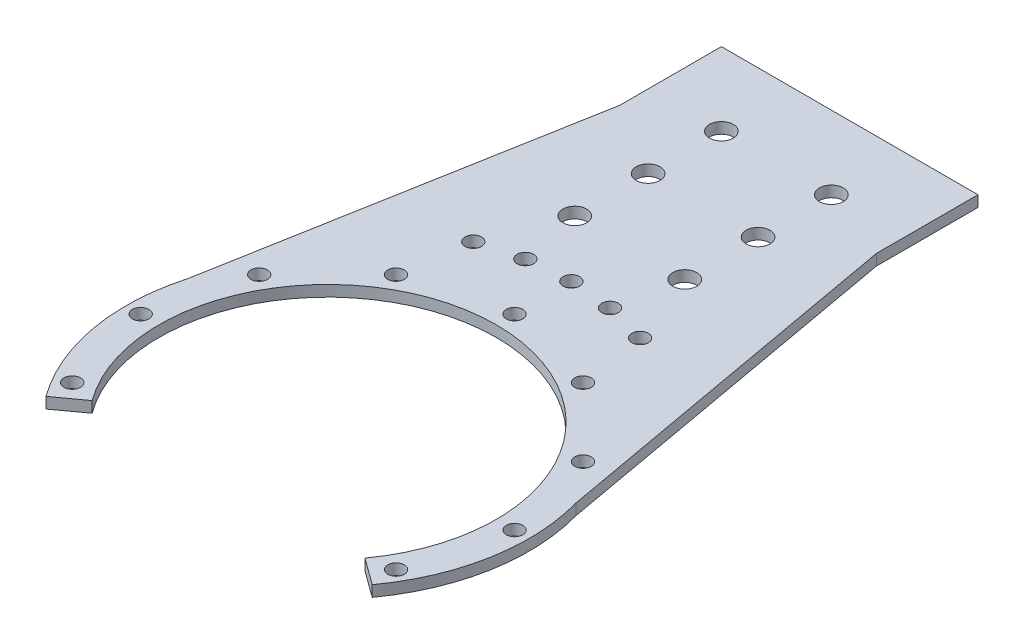
SolidWorks part; units mm, degrees
ref_plane "Front Plane" through (0, 0, 0) normal (0, 0, 1) x (1, 0, 0)
ref_plane "Top Plane" through (0, 0, 0) normal (0, 1, 0) x (1, 0, 0)
ref_plane "Right Plane" through (0, 0, 0) normal (1, 0, 0) x (0, 0, -1)
sketch "Sketch1" plane through (0, 0, 0) normal (0, 1, 0) x (1, 0, 0)
  circle A0 centre (0, 0) radius 55
  dimension "D1" = 110
extrude "Boss-Extrude1" add sketch "Sketch1" along normal blind 3
sketch "Sketch2" plane through (0, 0, 0) normal (0, 1, 0) x (1, 0, 0)
  line L0 (0, 0) -> (0, 92.4264) construction
  line L1 (-35, 142.4264) -> (-35, 42.4264)
  line L2 (-35, 142.4264) -> (35, 142.4264)
  line L3 (-35, 42.4264) -> (35, 42.4264)
  line L4 (35, 142.4264) -> (35, 42.4264)
  line L5 (0, 42.4264) -> (0, 142.4264) construction
  line L6 (-35, 92.4264) -> (35, 92.4264) construction
  circle A0 centre (0, 0) radius 55 construction
  dimension "D1" = 100
  dimension "D2" = 70
extrude "Boss-Extrude2" add sketch "Sketch2" along normal blind 3
sketch "Sketch9" plane through (0, 0, 0) normal (0, 1, 0) x (1, 0, 0)
  line L0 (-35, 114.7213) -> (-52.9849, 14.7514)
  line L1 (-35, 142.4264) -> (-35, 42.4264) construction
  line L2 (-52.9849, 14.7514) -> (-17.8715, 14.7514)
  line L3 (-17.8715, 14.7514) -> (-35, 114.7213)
  arc A0 (-35, 42.4264) -> (35, 42.4264) centre (0, 0) ccw construction
extrude "Boss-Extrude3" add sketch "Sketch9" along normal blind 3 contours L3 L0 L2
mirror "Mirror2" about plane through (0, 0, 0) normal (1, 0, 0) of "Boss-Extrude3"
sketch "Sketch4" plane through (0, 3, 0) normal (0, 1, 0) x (1, 0, 0)
  circle A0 centre (0, 0) radius 51 construction
  circle A1 centre (0, 0) radius 46
  dimension "D1" = 102
  dimension "D2" = 92
extrude "Cut-Extrude2" cut sketch "Sketch4" against normal through all both and the other way through all
sketch "Sketch7" plane through (0, 3, 0) normal (0, 1, 0) x (1, 0, 0)
  line L0 (0, 0) -> (0, -55)
  line L1 (0, 0) -> (-44.4959, -32.3282)
  arc A0 (-52.9849, 14.7514) -> (52.9849, 14.7514) centre (0, 0) ccw construction
  arc A1 (0, -55) -> (-44.4959, -32.3282) centre (0, 0) cw
  dimension "D1" = 54
extrude "Cut-Extrude5" cut sketch "Sketch7" against normal through all both and the other way through all
mirror "Mirror1" about plane through (0, 0, 0) normal (1, 0, 0) of "Cut-Extrude5"
sketch "Sketch5" plane through (0, 3, 0) normal (0, 1, 0) x (1, 0, 0)
  circle A0 centre (0, 0) radius 51 construction
  circle A1 centre (0, 51) radius 2.25
  dimension "D1" = 102
  dimension "D2" = 4.5
extrude "Cut-Extrude3" cut sketch "Sketch5" against normal through all both and the other way through all
pattern_circular "CirPattern1" count 12 over 360 about axis through (0, 0, 0) along (0, 1, 0) of "Cut-Extrude3"
sketch "Sketch6" plane through (0, 3, 0) normal (0, 1, 0) x (1, 0, 0)
  line L0 (0, 142.4264) -> (0, 0) construction
  line L1 (35, 142.4264) -> (-35, 142.4264) construction
  line L2 (-15, 122.4264) -> (15, 122.4264) construction
  circle A0 centre (15, 122.4264) radius 3.25
  circle A1 centre (-15, 122.4264) radius 3.25
  point P8 (0, 122.4264)
  dimension "D1" = 6.5
  dimension "D2" = 30
  dimension "D3" = 20
extrude "Cut-Extrude4" cut sketch "Sketch6" against normal through all both and the other way through all
pattern_linear "LPattern1" count 3 spacing 20 along (0, 0, 1) of "Cut-Extrude4"
sketch "Sketch8" plane through (0, 0, 0) normal (0, 1, 0) x (1, 0, 0)
  circle A0 centre (0, 0) radius 66.5 construction
  circle A1 centre (0, 66.5) radius 2.25
  dimension "D1" = 133
  dimension "D2" = 4.5
extrude "Cut-Extrude6" cut sketch "Sketch8" against normal through all both and the other way through all
pattern_circular "CirPattern2" count 3 every 10 about axis through (0, 0, 0) along (0, 1, 0) of "Cut-Extrude6"
